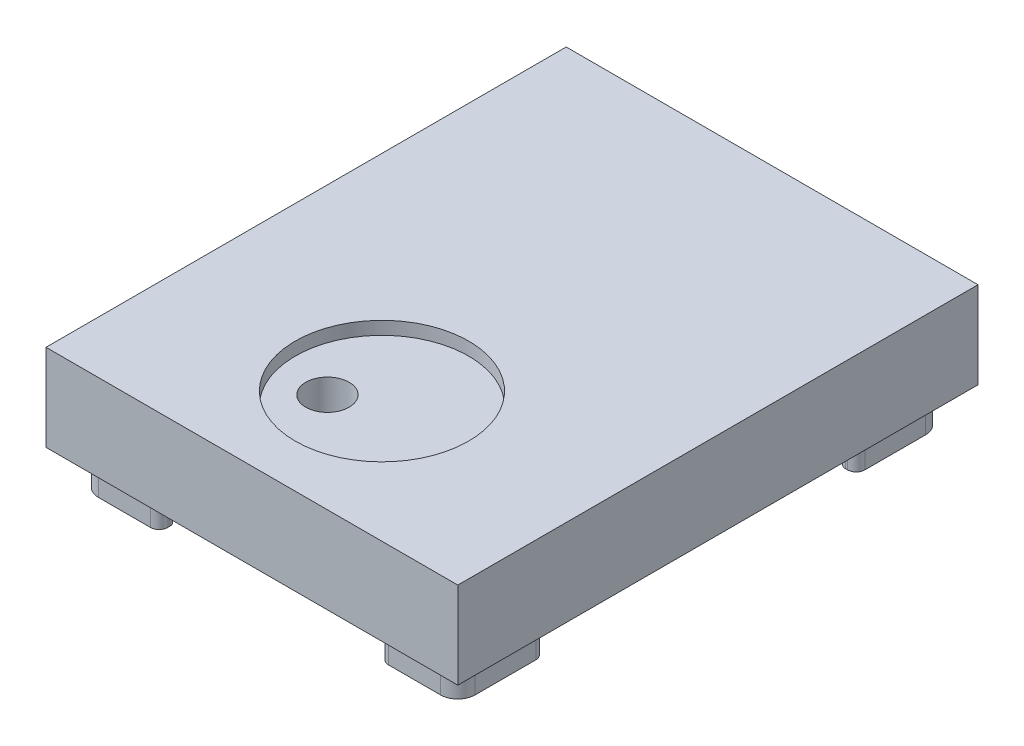
SolidWorks part; units mm, degrees
ref_plane "Front Plane" through (0, 0, 0) normal (0, 0, 1) x (1, 0, 0)
ref_plane "Top Plane" through (0, 0, 0) normal (0, 1, 0) x (1, 0, 0)
ref_plane "Right Plane" through (0, 0, 0) normal (1, 0, 0) x (0, 0, -1)
sketch "Sketch2" plane through (0, 0, 0) normal (0, 1, 0) x (1, 0, 0)
  line L1 (-47.5, -60) -> (47.5, -60)
  line L2 (-47.5, -60) -> (-47.5, 60)
  line L3 (-47.5, 60) -> (47.5, 60)
  line L4 (47.5, -60) -> (47.5, 60)
  line L5 (-47.5, -60) -> (47.5, 60) construction
  line L6 (-47.5, 60) -> (47.5, -60) construction
  point P0 (0, 0)
  dimension "D1" = 120
  dimension "D2" = 95
extrude "top plate" add sketch "Sketch2" along normal blind 20
sketch "Sketch3" plane through (0, 0, 0) normal (0, -1, 0) x (1, 0, 0)
  line L0 (-37.45, 51.95) -> (-26.95, 51.95)
  line L3 (-41.45, 35.95) -> (-40.95, 35.95)
  line L10 (-25.45, 53.95) -> (-25.45, 53.45)
  line L11 (-27.45, 55.95) -> (-39.45, 55.95)
  line L12 (-43.45, 51.95) -> (-43.45, 37.95)
  line L13 (-47.5, 60) -> (47.5, 60) construction
  line L14 (-47.5, -60) -> (-47.5, 60) construction
  line L15 (-39.45, 49.95) -> (-39.45, 37.45)
  arc A0 (-43.45, 51.95) -> (-39.45, 55.95) centre (-39.45, 51.95) cw
  arc A1 (-25.45, 53.95) -> (-27.45, 55.95) centre (-27.45, 53.95) ccw
  arc A2 (-39.45, 49.95) -> (-37.45, 51.95) centre (-37.45, 49.95) cw
  arc A3 (-40.95, 35.95) -> (-39.45, 37.45) centre (-40.95, 37.45) ccw
  arc A4 (-26.95, 51.95) -> (-25.45, 53.45) centre (-26.95, 53.45) ccw
  arc A5 (-43.45, 37.95) -> (-41.45, 35.95) centre (-41.45, 37.95) ccw
  point P12 (-43.45, 55.95)
  point P23 (-43.45, 35.95)
  dimension "D7" = 4
  dimension "D8" = 2
  dimension "D9" = 2
  dimension "D10" = 1.5
  dimension "D11" = 2
  dimension "D1" = 4.05
  dimension "D2" = 20
  dimension "D3" = 4
  dimension "D4" = 4.05
  dimension "D5" = 18
  dimension "D6" = 4
extrude "friction clip" add sketch "Sketch3" along normal blind 8
mirror "4 clips" about plane through (0, 0, 0) normal (0, 0, 1) of "friction clip" second plane through (0, 0, 0) second plane normal (1, 0, 0)
sketch "Sketch8" plane through (0, 0, 0) normal (0, -1, 0) x (1, 0, 0)
  line L1 (-36.8642, -51.3642) -> (36.8642, -51.3642)
  line L2 (-38.8642, -49.3642) -> (-38.8642, 49.3642)
  line L3 (-36.8642, 51.3642) -> (36.8642, 51.3642)
  line L4 (38.8642, -49.3642) -> (38.8642, 49.3642)
  line L5 (-38.8642, -51.3642) -> (38.8642, 51.3642) construction
  line L6 (-38.8642, 51.3642) -> (38.8642, -51.3642) construction
  arc A0 (39.45, 49.95) -> (37.45, 51.95) centre (37.45, 49.95) ccw construction
  arc A1 (36.8642, -51.3642) -> (38.8642, -49.3642) centre (36.8642, -49.3642) ccw
  arc A2 (-36.8642, -51.3642) -> (-38.8642, -49.3642) centre (-36.8642, -49.3642) cw
  arc A3 (-38.8642, 49.3642) -> (-36.8642, 51.3642) centre (-36.8642, 49.3642) cw
  arc A4 (36.8642, 51.3642) -> (38.8642, 49.3642) centre (36.8642, 49.3642) cw
  point P0 (0, 0)
  dimension "D1" = 2
extrude "Cut-Extrude1" cut sketch "Sketch8" against normal blind 15
sketch "Sketch5" plane through (0, 20, 0) normal (0, 1, 0) x (1, 0, 0)
  line L0 (-47.5, -60) -> (47.5, -60) construction
  line L1 (-47.5, 60) -> (-47.5, -60) construction
  circle A0 centre (-8.56, -34.015) radius 5
  dimension "D3" = 10
  dimension "D1" = 25.985
  dimension "D2" = 38.94
extrude "snooze hole" cut sketch "Sketch5" against normal through all
sketch "Sketch6" plane through (0, 0, 0) normal (0, -1, 0) x (1, 0, 0)
  circle A0 centre (-8.56, 34.015) radius 5 construction
  circle A1 centre (-8.56, 34.015) radius 5
  circle A2 centre (-8.56, 34.015) radius 8
  dimension "D1" = 16
extrude "snooze hole support" add sketch "Sketch6" along normal blind 15 and the other way blind 15
sketch "Sketch9" plane through (0, 20, 0) normal (0, 1, 0) x (1, 0, 0)
  line L0 (0, -15.4) -> (0, 15.4) construction
  line L1 (-47.5, -60) -> (47.5, -60) construction
  circle A0 centre (0, -30) radius 20
  dimension "D1" = 30
  dimension "D2" = 40
extrude "lake inlay" cut sketch "Sketch9" against normal blind 3
